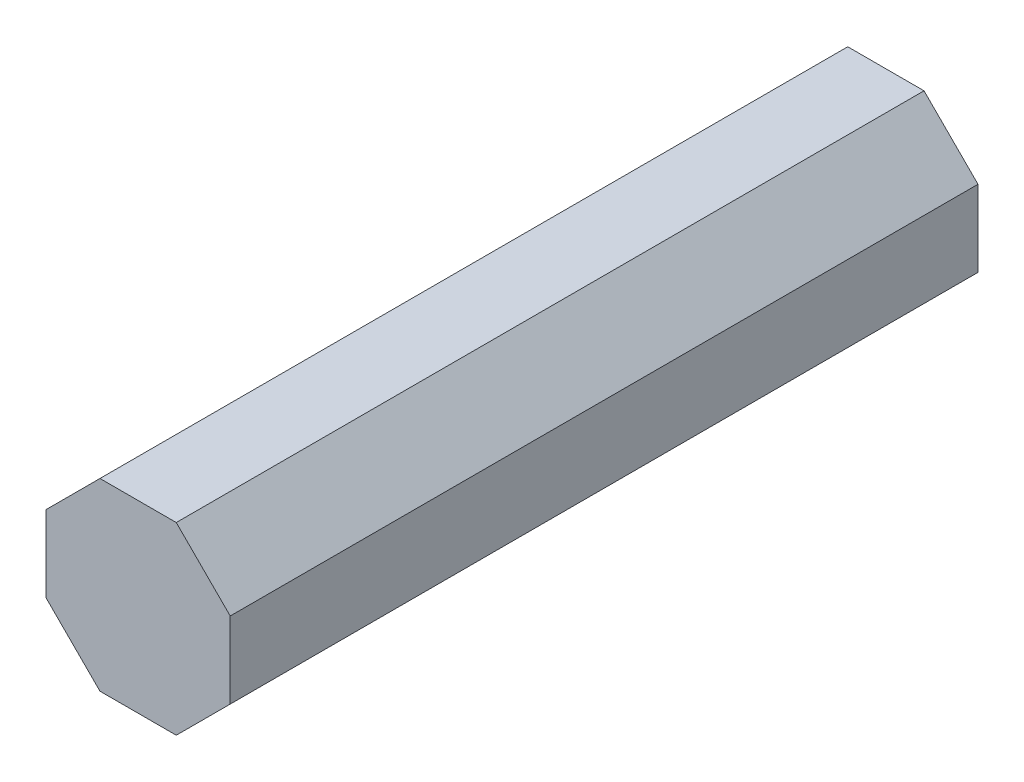
SolidWorks part; units mm, degrees
ref_plane "Front Plane" through (0, 0, 0) normal (0, 0, 1) x (1, 0, 0)
ref_plane "Top Plane" through (0, 0, 0) normal (0, 1, 0) x (1, 0, 0)
ref_plane "Right Plane" through (0, 0, 0) normal (1, 0, 0) x (0, 0, -1)
sketch "Sketch2" plane through (0, 0, 0) normal (0, 0, 1) x (1, 0, 0)
  line L1 (1.5307, 3.6955) -> (-1.5307, 3.6955)
  line L2 (-1.5307, 3.6955) -> (-3.6955, 1.5307)
  line L3 (-3.6955, 1.5307) -> (-3.6955, -1.5307)
  line L4 (-3.6955, -1.5307) -> (-1.5307, -3.6955)
  line L5 (-1.5307, -3.6955) -> (1.5307, -3.6955)
  line L6 (1.5307, -3.6955) -> (3.6955, -1.5307)
  line L7 (3.6955, -1.5307) -> (3.6955, 1.5307)
  line L8 (3.6955, 1.5307) -> (1.5307, 3.6955)
  circle A0 centre (0, 0) radius 4 construction
  circle A1 centre (0, 0) radius 3.6955 construction
  point P3 (3.6955, 1.5307)
  dimension "D1" = 8
extrude "Boss-Extrude1" add sketch "Sketch2" along normal blind 30
